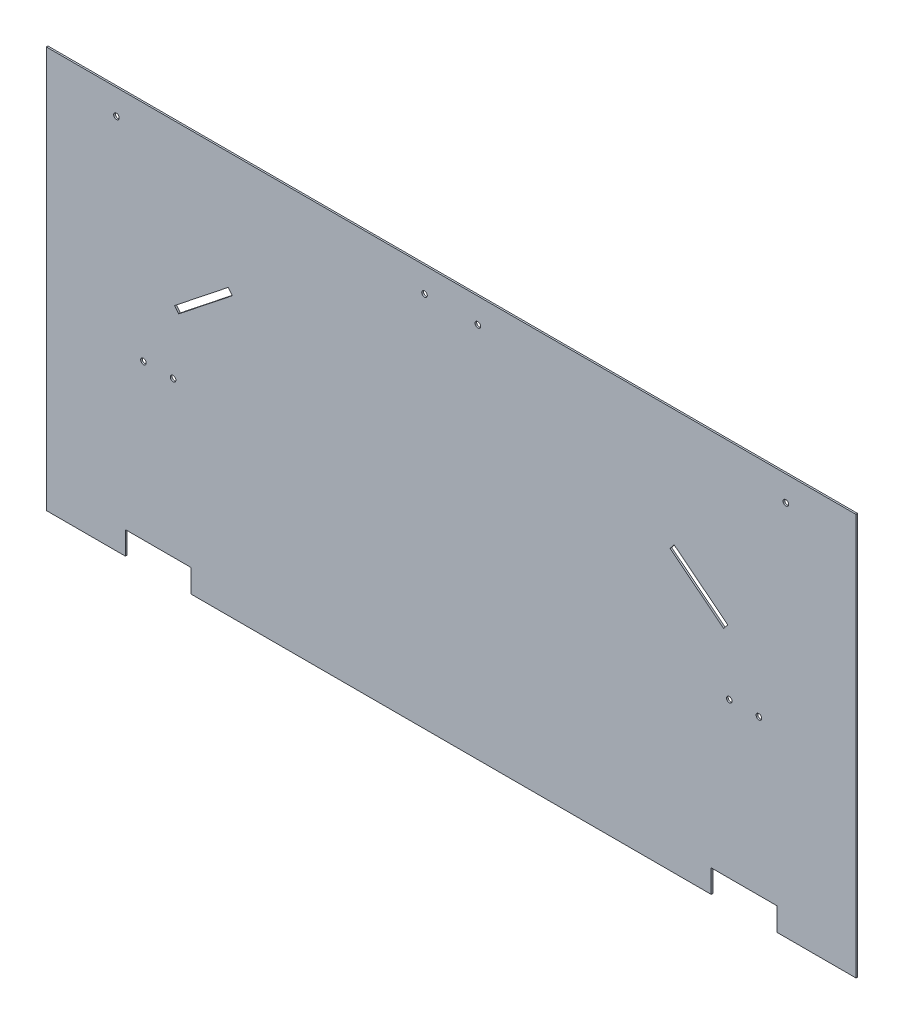
SolidWorks part; units mm, degrees
material "PE High Density"
ref_plane "Front Plane" through (0, 0, 0) normal (0, 0, 1) x (1, 0, 0)
ref_plane "Top Plane" through (0, 0, 0) normal (0, 1, 0) x (1, 0, 0)
ref_plane "Right Plane" through (0, 0, 0) normal (1, 0, 0) x (0, 0, -1)
sketch "Sketch1" plane through (0, 0, 0) normal (0, 0, 1) x (1, 0, 0)
  line L1 (-781.05, 387.35) -> (781.05, 387.35)
  line L2 (-781.05, 387.35) -> (-781.05, -387.35)
  line L3 (-781.05, -387.35) -> (781.05, -387.35)
  line L4 (781.05, 387.35) -> (781.05, -387.35)
  line L5 (-781.05, 387.35) -> (781.05, -387.35) construction
  line L6 (-781.05, -387.35) -> (781.05, 387.35) construction
  line L7 (-533.6334, 78.9622) -> (-525.7417, 69.0118)
  line L8 (-542.925, 342.9) -> (-542.925, -501.65) construction
  line L9 (542.925, 342.9) -> (542.925, -501.65) construction
  line L11 (587.375, 342.9) -> (587.375, -501.65) construction
  line L12 (-587.375, 342.9) -> (-587.375, -501.65) construction
  line L21 (-628.65, -387.35) -> (-501.65, -387.35)
  line L22 (-628.65, -387.35) -> (-628.65, -342.9)
  line L23 (-628.65, -342.9) -> (-501.65, -342.9)
  line L24 (-501.65, -387.35) -> (-501.65, -342.9)
  line L25 (628.65, -387.35) -> (501.65, -387.35)
  line L26 (628.65, -387.35) -> (628.65, -342.9)
  line L27 (628.65, -342.9) -> (501.65, -342.9)
  line L28 (501.65, -387.35) -> (501.65, -342.9)
  line L32 (-525.7417, 69.0118) -> (-422.2573, 151.0856)
  line L33 (-422.2573, 151.0856) -> (-430.149, 161.036)
  line L34 (-430.149, 161.036) -> (-533.6334, 78.9622)
  line L36 (525.8301, 69.1038) -> (422.2669, 151.078)
  line L37 (422.2669, 151.078) -> (430.149, 161.036)
  line L38 (430.149, 161.036) -> (533.7123, 79.0618)
  line L39 (533.7123, 79.0618) -> (525.8301, 69.1038)
  circle A0 centre (-51.435, 339.4592) radius 5.3578
  circle A1 centre (51.435, 339.3385) radius 5.3578
  circle A6 centre (-645.795, 339.09) radius 5.3578
  circle A7 centre (645.795, 339.09) radius 5.3578
  circle A11 centre (536.575, -44.45) radius 5.3578
  circle A12 centre (593.725, -44.45) radius 5.3578
  circle A13 centre (-593.725, -44.45) radius 5.3578
  circle A14 centre (-536.575, -44.45) radius 5.3578
  point P0 (0, 0)
  dimension "D3" = 10.7156
  dimension "D4" = 10.7156
  dimension "D7" = 729.615
  dimension "D8" = 729.615
  dimension "D19" = 135.255
  dimension "D20" = 48.26
  dimension "D21" = 10.7156
  dimension "D22" = 135.255
  dimension "D23" = 48.26
  dimension "D38" = 342.9
  dimension "D39" = 342.9
  dimension "D40" = 6.35
  dimension "D9" = 47.8908
  dimension "D14" = 350.901
  dimension "D24" = 10.7156
  dimension "D31" = 10.7156
  dimension "D32" = 10.7156
  dimension "D33" = 10.7156
  dimension "D34" = 10.7156
  dimension "D1" = 774.7
  dimension "D2" = 1562.1
  dimension "D10" = 48.0115
  dimension "D11" = 226.314
  dimension "D12" = 350.901
  dimension "D13" = 226.314
  dimension "D35" = 6.35
  dimension "D36" = 6.35
  dimension "D37" = 342.9
  dimension "D41" = 342.9
  dimension "D42" = 6.35
  dimension "D52" = 152.4
  dimension "D53" = 127
  dimension "D54" = 44.45
  dimension "D55" = 152.4
  dimension "D56" = 127
  dimension "D57" = 44.45
  dimension "D63" = 132.08
  dimension "D64" = 12.7
  dimension "D65" = 132.08
  dimension "D66" = 12.7
extrude "Boss-Extrude1" add sketch "Sketch1" along normal blind 3.175
sketch "Sketch2" plane through (0, 0, 3.175) normal (0, 0, 1) x (1, 0, 0)
  line L2 (781.05, 387.35) -> (781.05, -387.35) construction
  line L3 (628.65, -387.35) -> (781.05, -387.35) construction
  line L4 (-781.05, 387.35) -> (781.05, 387.35) construction
  line L5 (-781.05, 387.35) -> (-781.05, -387.35) construction
  line L7 (-781.05, -387.35) -> (-628.65, -387.35) construction
  circle A0 centre (-313.055, 258.318) radius 5.3578
  circle A1 centre (-292.227, 234.3543) radius 5.3578
  circle A2 centre (-690.753, -42.672) radius 5.3578
  circle A3 centre (-671.703, -68.072) radius 5.3578
  circle A4 centre (292.227, 234.3543) radius 5.3578
  circle A5 centre (313.055, 258.318) radius 5.3578
  circle A6 centre (690.753, -42.672) radius 5.3578
  circle A7 centre (671.703, -68.072) radius 5.3578
  dimension "D1" = 10.7156
  dimension "D3" = 31.75
  dimension "D8" = 129.032
  dimension "D2" = 90.297
  dimension "D4" = 344.678
  dimension "D5" = 109.347
  dimension "D6" = 31.75
  dimension "D7" = 467.995
  dimension "D9" = 488.823
  dimension "D10" = 467.995
  dimension "D11" = 488.823
  dimension "D12" = 129.032
  dimension "D13" = 31.75
  dimension "D14" = 90.297
  dimension "D15" = 109.347
  dimension "D16" = 344.678
  dimension "D17" = 31.75
sketch "Sketch4" plane through (0, 0, 3.175) normal (0, 0, 1) x (1, 0, 0)
  line L0 (-781.05, 387.35) -> (781.05, 387.35) construction
  point P0 (-565.15, 266.7)
  point P1 (565.15, 266.7)
  dimension "D1" = 1130.3
  dimension "D2" = 565.15
  dimension "D3" = 120.65
equation "\"D2@Sketch4\"=\"D1@Sketch4\"/2"
